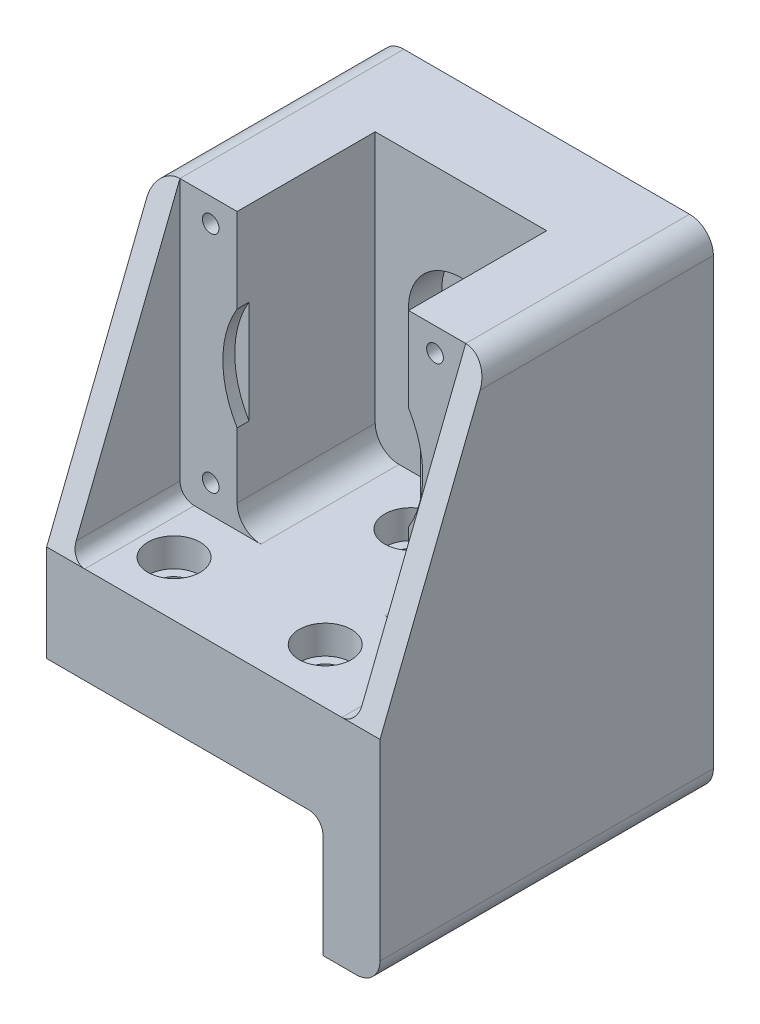
SolidWorks part; units mm, degrees
ref_plane "Front Plane" through (0, 0, 0) normal (0, 0, 1) x (1, 0, 0)
ref_plane "Top Plane" through (0, 0, 0) normal (0, 1, 0) x (1, 0, 0)
ref_plane "Right Plane" through (0, 0, 0) normal (1, 0, 0) x (0, 0, -1)
sketch "Sketch1" plane through (0, 0, 0) normal (0, 0, 1) x (1, 0, 0)
  line L0 (-35, -74.75) -> (-35, 28.55)
  line L1 (-23.55, -23.55) -> (23.55, -23.55) construction
  line L2 (-23.55, -23.55) -> (-23.55, 23.55) construction
  line L3 (-23.55, 23.55) -> (23.55, 23.55) construction
  line L4 (23.55, -23.55) -> (23.55, 23.55) construction
  line L5 (-23.55, -23.55) -> (23.55, 23.55) construction
  line L6 (-23.55, 23.55) -> (23.55, -23.55) construction
  line L7 (-35, 28.55) -> (35, 28.55)
  line L8 (35, 28.55) -> (35, -74.75)
  line L9 (35, -74.75) -> (23, -74.75)
  line L10 (23, -74.75) -> (23, -49.75)
  line L11 (23, -49.75) -> (-23, -49.75)
  line L12 (-23, -49.75) -> (-23, -74.75)
  line L13 (-23, -74.75) -> (-35, -74.75)
  line L14 (0, -49.75) -> (0, 28.55) construction
  line L15 (-35, -30) -> (35, -30) construction
  circle A0 centre (-23.55, 23.55) radius 1.75
  circle A1 centre (23.55, -23.55) radius 1.75
  circle A2 centre (23.55, 23.55) radius 1.75
  circle A3 centre (-23.55, -23.55) radius 1.75
  circle A4 centre (0, 0) radius 6
  point P0 (0, 0)
  dimension "D1" = 3.5
  dimension "D9" = 12
  dimension "D2" = 47.1
  dimension "D3" = 70
  dimension "D4" = 46
  dimension "D5" = 5
  dimension "D6" = 30
  dimension "D7" = 49.75
  dimension "D8" = 25
extrude "Boss-Extrude1" add sketch "Sketch1" along normal blind 70
sketch "Sketch2" plane through (0, 0, 70) normal (0, 0, 1) x (1, 0, 0)
  line L0 (-18, 28.55) -> (-18, -29.45)
  line L1 (35, 28.55) -> (-35, 28.55) construction
  line L2 (-18, -29.45) -> (18, -29.45)
  line L3 (18, -29.45) -> (18, 28.55)
  line L4 (-18, 28.55) -> (18, 28.55)
  line L5 (0, 0) -> (0, -29.45) construction
  dimension "D1" = 58
  dimension "D2" = 36
extrude "Cut-Extrude1" cut sketch "Sketch2" against normal offset from surface (52 mm away) 18 up to face at (-21.8, -23.55, 0)
sketch "Sketch3" plane through (0, 0, 70) normal (0, 0, 1) x (1, 0, 0)
  line L0 (-30, 28.55) -> (-30, -29.45)
  line L1 (-18, 28.55) -> (-35, 28.55) construction
  line L2 (-30, -29.45) -> (30, -29.45)
  line L3 (30, -29.45) -> (30, 28.55)
  line L4 (35, 28.55) -> (18, 28.55) construction
  line L5 (-18, -29.45) -> (18, -29.45) construction
  line L6 (0, 0) -> (0, -29.45)
  line L7 (-18, -29.45) -> (18, -29.45) construction
  line L8 (-30, 28.55) -> (30, 28.55)
  dimension "D1" = 60
extrude "Cut-Extrude2" cut sketch "Sketch3" against normal offset from surface (23 mm away) 29 contours L0 L2 L3 L8 up to face at (-6, 0, 18)
sketch "Sketch4" plane through (0, 0, 47) normal (0, 0, 1) x (1, 0, 0)
  circle A0 centre (0, 0) radius 21
  dimension "D1" = 42
extrude "Cut-Extrude3" cut sketch "Sketch4" against normal blind 2.5
fillet "Fillet2" radius 5 6 edges at (35, -74.75, 35) (-35, -74.75, 35) (35, 28.55, 35) (-35, 28.55, 35) (18, -29.45, 32.5) (-18, -29.45, 32.5)
fillet "Fillet3" radius 3 4 edges at (23, -49.75, 35) (-23, -49.75, 35) (30, -29.45, 58.5) (-30, -29.45, 58.5)
sketch "Sketch5" plane through (0, 0, 18) normal (0, 0, 1) x (1, 0, 0)
  circle A0 centre (0, 0) radius 11.025
  dimension "D1" = 22.05
extrude "Cut-Extrude4" cut sketch "Sketch5" against normal blind 7
hole_wizard "CBORE for M6 Socket Head Cap Screw1" positions "Sketch6" profile "Sketch7" counterbore size "M6" standard "IS" end condition through all
sketch "Sketch6" plane through (0, -29.45, 0) normal (0, 1, 0) x (1, 0, 0)
  line L0 (0, -28.5) -> (0, -58.5) construction
  line L2 (-19.75, -58.5) -> (12, -58.5) construction
  line L4 (-30, -47) -> (-18, -47) construction
  line L5 (-27, -70) -> (27, -70) construction
  line L8 (-18, -47) -> (-18, -18) construction
  line L9 (18, -18) -> (18, -47) construction
  point P0 (0, -28.5)
  point P2 (-19.75, -58.5)
  point P4 (12, -58.5)
  dimension "D1" = 30
  dimension "D2" = 31.75
  dimension "D3" = 12
sketch "Sketch7" plane through (0, -29.45, 28.5) normal (1, 0, 0) x (0, 0, 1)
  line L0 (0, 0) -> (0, 45.3)
  line L1 (0, 45.3) -> (3.5, 45.3)
  line L3 (3.5, 45.3) -> (3.5, 6)
  line L4 (3.5, 6) -> (5.5, 6)
  line L5 (5.5, 6) -> (5.5, 0)
  line L7 (5.5, 0) -> (0, 0)
  line L11 (0, -6.35) -> (0, 107.95) construction
  dimension "Thru Hole Dia." = 7
  dimension "Thru Hole Depth" = 45.3
  dimension "C'Bore Dia." = 11
  dimension "C'Bore Depth" = 6
sketch "Sketch8" plane through (0, 0, 70) normal (0, 0, 1) x (1, 0, 0)
  line L0 (-20, -49.75) -> (20, -49.75) construction
  line L1 (-4.1155, -49.75) -> (-63.7899, -49.75)
  line L2 (-4.1155, -49.75) -> (-4.1155, -81.1968)
  line L3 (-4.1155, -81.1968) -> (-63.7899, -81.1968)
  line L4 (-63.7899, -49.75) -> (-63.7899, -81.1968)
extrude "Cut-Extrude5" cut sketch "Sketch8" against normal through all
sketch "Sketch9" plane through (0, 0, 0) normal (1, 0, 0) x (0, 0, -1)
  line L0 (-47, 28.55) -> (-70, 28.55)
  line L1 (-70, 28.55) -> (-70, -29.45)
  line L2 (-70, -69.75) -> (-70, 23.55) construction
  line L3 (-70, -29.45) -> (-47, 28.55)
extrude "Cut-Extrude6" cut sketch "Sketch9" against normal through all both and the other way through all
chamfer "Chamfer1" distance 1 angle 45 1 edges at (6, 0, 11)
